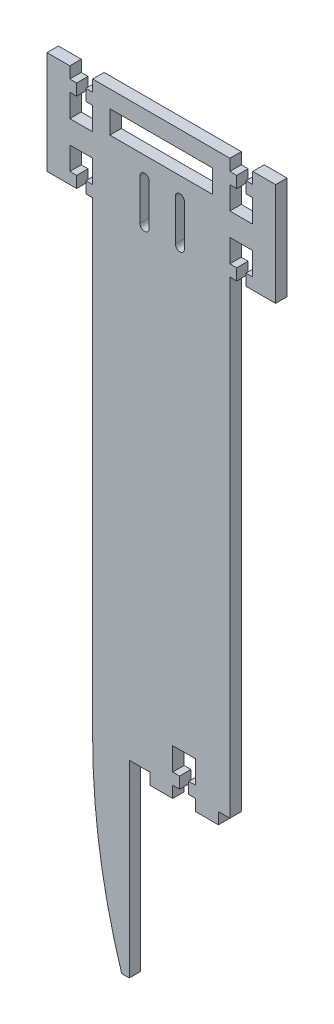
SolidWorks part; units mm, degrees
ref_plane "Front Plane" through (0, 0, 0) normal (0, 0, 1) x (1, 0, 0)
ref_plane "Top Plane" through (0, 0, 0) normal (0, 1, 0) x (1, 0, 0)
ref_plane "Right Plane" through (0, 0, 0) normal (1, 0, 0) x (0, 0, -1)
sketch "Sketch1" plane through (0, 0, 0) normal (0, 0, 1) x (1, 0, 0)
  line L0 (0, 0) -> (100, 0)
  line L1 (0, 0) -> (0, 40)
  line L3 (0, 40) -> (100, 40)
  line L4 (0, 40) -> (10, 40)
  line L5 (0, 40) -> (0, 45)
  line L6 (10, 40) -> (10, 45)
  line L7 (0, 45) -> (10, 45)
  line L8 (20, 40) -> (80, 40)
  line L9 (20, 40) -> (20, 45)
  line L11 (20, 45) -> (80, 45)
  line L12 (50, 40) -> (50, 27.4155) construction
  line L17 (0, 20) -> (11.6683, 20) construction
  line L23 (20, -5) -> (80, -5)
  line L24 (20, 0) -> (20, -5)
  line L25 (20, 0) -> (80, 0)
  line L26 (10, 0) -> (10, -5)
  line L27 (0, -5) -> (10, -5)
  line L28 (0, 0) -> (0, -5)
  line L29 (0, 0) -> (10, 0)
  line L30 (17, 40) -> (17, 35)
  line L31 (17, 40) -> (13, 40)
  line L32 (17, 35) -> (13, 35)
  line L33 (13, 40) -> (13, 35)
  line L34 (10, 35) -> (20, 35)
  line L35 (10, 35) -> (10, 25)
  line L36 (20, 35) -> (20, 25)
  line L37 (10, 25) -> (20, 25)
  line L38 (10, 45) -> (20, 45) construction
  line L55 (17, 5) -> (13, 5)
  line L56 (13, 0) -> (13, 5)
  line L57 (17, 0) -> (13, 0)
  line L58 (17, 0) -> (17, 5)
  line L59 (20, 5) -> (20, 15)
  line L60 (10, 15) -> (20, 15)
  line L61 (10, 5) -> (10, 15)
  line L62 (10, 5) -> (20, 5)
  line L64 (50, 45) -> (50, 40)
  line L65 (90, 45) -> (80, 45) construction
  line L66 (50, 0) -> (50, -5)
  line L67 (100, 20) -> (88.3317, 20) construction
  line L68 (90, 5) -> (80, 5)
  line L69 (90, 5) -> (90, 15)
  line L70 (90, 15) -> (80, 15)
  line L71 (80, 5) -> (80, 15)
  line L72 (83, 0) -> (83, 5)
  line L73 (83, 0) -> (87, 0)
  line L74 (87, 0) -> (87, 5)
  line L75 (83, 5) -> (87, 5)
  line L76 (90, 25) -> (80, 25)
  line L77 (80, 35) -> (80, 25)
  line L78 (90, 35) -> (90, 25)
  line L79 (90, 35) -> (80, 35)
  line L80 (87, 40) -> (87, 35)
  line L81 (83, 35) -> (87, 35)
  line L82 (83, 40) -> (87, 40)
  line L83 (83, 40) -> (83, 35)
  line L84 (100, 0) -> (90, 0)
  line L85 (100, 0) -> (100, -5)
  line L86 (100, -5) -> (90, -5)
  line L87 (90, 0) -> (90, -5)
  line L88 (80, 0) -> (80, -5)
  line L89 (80, 40) -> (80, 45)
  line L90 (100, 45) -> (90, 45)
  line L91 (90, 40) -> (90, 45)
  line L92 (100, 40) -> (100, 45)
  line L93 (100, 40) -> (90, 40)
  line L94 (100, 0) -> (100, 40)
  point P29 (15, 35)
  point P36 (15, 35)
  point P39 (15, 45)
  dimension "D1" = 40
  dimension "D2" = 30
  dimension "D3" = 10
  dimension "D4" = 5
  dimension "D5" = 5
  dimension "D7" = 10
  dimension "D8" = 4
  dimension "D9" = 5
  dimension "D10" = 10
  dimension "D11" = 10
  dimension "D12" = 5
extrude "Boss-Extrude1" add sketch "Sketch1" against normal blind 5 contours L3 L92 L90 L91 | L0 L94 L3 L80 L79 L78 L76 L77 L83 L8 L30 L34 L36 L37 L35 L33 L1 L56 L62 L61 L60 L59 L58 L25 L72 L68 L71 L70 L69 L74 | L8 L89 L11 L64 | L64 L11 L9 L3 | L7 L5 L3 L6 | L0 L28 L27 L26 | L66 L0 L24 L23 | L88 L25 L66 L23 | L0 L87 L86 L85
sketch "Sketch4" plane through (0, 0, -5) normal (0, 0, -1) x (-1, 0, 0)
  line L0 (-58.15, 0.6395) -> (-58.15, 18.6395) construction
  line L1 (-60.15, 0.6395) -> (-60.15, 18.6395)
  line L2 (-56.15, 0.6395) -> (-56.15, 18.6395)
  line L5 (-42.65, 0.6395) -> (-42.65, 18.6395) construction
  line L6 (-44.65, 0.6395) -> (-44.65, 18.6395)
  line L7 (-40.65, 0.6395) -> (-40.65, 18.6395)
  line L8 (-100, -5) -> (-100, 45) construction
  arc A0 (-60.15, 0.6395) -> (-56.15, 0.6395) centre (-58.15, 0.6395) ccw
  arc A1 (-56.15, 18.6395) -> (-60.15, 18.6395) centre (-58.15, 18.6395) ccw
  arc A2 (-44.65, 0.6395) -> (-40.65, 0.6395) centre (-42.65, 0.6395) ccw
  arc A3 (-40.65, 18.6395) -> (-44.65, 18.6395) centre (-42.65, 18.6395) ccw
  point P2 (-58.15, 9.6395)
  point P15 (-42.65, 9.6395)
  dimension "D2" = 2
  dimension "D1" = 18
  dimension "D3" = 39.85
  dimension "D5" = 2
extrude "Cut-Extrude3" cut sketch "Sketch4" against normal blind 5
sketch "Sketch5" plane through (0, 0, -5) normal (0, 0, -1) x (-1, 0, 0)
  line L0 (-20, 45) -> (-80, 45) construction
  line L1 (-72.5, 37.5) -> (-27.5, 37.5)
  line L2 (-72.5, 37.5) -> (-72.5, 27.5)
  line L3 (-72.5, 27.5) -> (-27.5, 27.5)
  line L4 (-27.5, 37.5) -> (-27.5, 27.5)
  point P4 (-50, 37.5)
  point P7 (-50, 45)
  dimension "D1" = 45
  dimension "D2" = 10
  dimension "D3" = 7.5
extrude "Cut-Extrude4" cut sketch "Sketch5" against normal blind 10
sketch "Sketch6" plane through (0, 0, 0) normal (0, 0, 1) x (1, 0, 0)
  line L1 (100, -5) -> (100, 45) construction
  line L2 (0, -5) -> (10, -5)
  line L3 (0, -5) -> (0, 0)
  line L4 (0, 0) -> (10, 0)
  line L5 (10, -5) -> (10, 0)
  line L6 (90, -5) -> (100, -5)
  line L7 (90, -5) -> (90, 0)
  line L8 (90, 0) -> (100, 0)
  line L9 (100, -5) -> (100, 0)
extrude "Cut-Extrude5" cut sketch "Sketch6" against normal blind 5
sketch "Sketch7" plane through (0, -5, 0) normal (0, -1, 0) x (1, 0, 0)
  line L4 (80, 0) -> (20, 0)
  line L5 (20, 0) -> (20, -5)
  line L6 (20, -5) -> (80, -5)
  line L7 (80, -5) -> (80, 0)
  line L8 (80, 0) -> (20, 0)
  line L9 (20, 0) -> (20, -5)
  line L10 (20, -5) -> (80, -5)
  line L11 (80, -5) -> (80, 0)
  dimension "D1" = 0
extrude "Boss-Extrude2" add sketch "Sketch7" along normal blind 200
sketch "Sketch8" plane through (0, 0, 0) normal (0, 0, 1) x (1, 0, 0)
  line L0 (80, -205) -> (20, -205) construction
  line L1 (45, -205) -> (55, -205)
  line L2 (45, -205) -> (45, -210)
  line L3 (45, -210) -> (55, -210)
  line L4 (55, -205) -> (55, -210)
  line L5 (80, 0) -> (80, -205) construction
  line L6 (65, -205) -> (75, -205)
  line L7 (65, -205) -> (65, -210)
  line L8 (65, -210) -> (75, -210)
  line L9 (75, -205) -> (75, -210)
  dimension "D1" = 5
  dimension "D2" = 5
  dimension "D3" = 10
  dimension "D4" = 10
  dimension "D5" = 10
  dimension "D6" = 5
extrude "Boss-Extrude3" add sketch "Sketch8" against normal blind 5
sketch "Sketch9" plane through (0, 0, 0) normal (0, 0, 1) x (1, 0, 0)
  line L0 (65, -205) -> (55, -205) construction
  line L1 (58, -205) -> (62, -205)
  line L2 (58, -205) -> (58, -200)
  line L3 (58, -200) -> (62, -200)
  line L4 (62, -205) -> (62, -200)
  line L6 (55, -200) -> (65, -200)
  line L7 (55, -200) -> (55, -190)
  line L8 (55, -190) -> (65, -190)
  line L9 (65, -200) -> (65, -190)
  point P11 (60, -200)
  point P12 (60, -200)
  point P14 (60, -205)
  point P15 (60, -205)
  dimension "D1" = 10
  dimension "D2" = 10
  dimension "D3" = 5
  dimension "D4" = 4
extrude "Cut-Extrude6" cut sketch "Sketch9" against normal blind 5 contours L6 L9 L8 L7 L3 | L1 L4 L3 L2
sketch "Sketch10" plane through (0, 0, -5) normal (0, 0, -1) x (-1, 0, 0)
  line L0 (-20, -205) -> (-45, -205) construction
  line L2 (-36, -287.5) -> (-32.6667, -287.5)
  line L3 (-36, -287.5) -> (-36, -205)
  line L4 (-36, -205) -> (-20, -205)
  arc A0 (-32.6667, -287.5) -> (-20, -205) centre (-295, -205) ccw
  dimension "D1" = 550
  dimension "D2" = 82.5
  dimension "D3" = 16
extrude "Boss-Extrude4" add sketch "Sketch10" against normal blind 5
